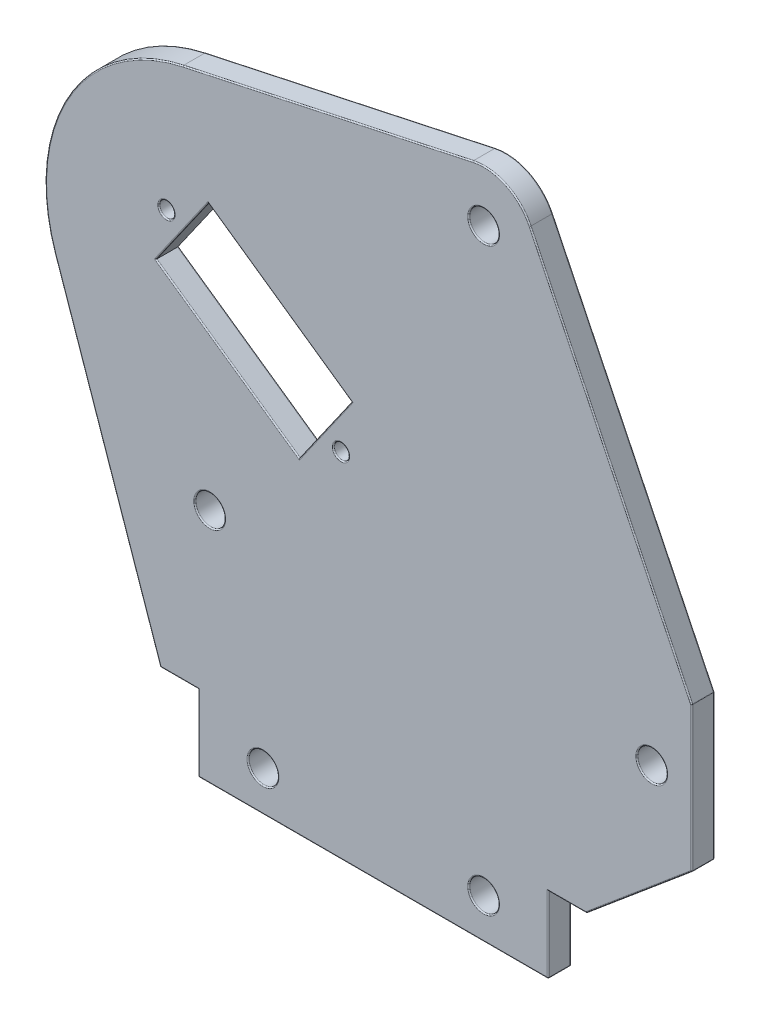
SolidWorks part; units mm, degrees
ref_plane "Płaszczyzna przednia" through (0, 0, 0) normal (0, 0, 1) x (1, 0, 0)
ref_plane "Płaszczyzna górna" through (0, 0, 0) normal (0, 1, 0) x (1, 0, 0)
ref_plane "Płaszczyzna prawa" through (0, 0, 0) normal (1, 0, 0) x (0, 0, -1)
sketch "Szkic1" plane through (0, 0, 0) normal (0, 0, 1) x (1, 0, 0)
  line L0 (28, 10) -> (41.85, 21.6215) construction
  line L1 (23, 10) -> (28, 10) construction
  line L2 (23, 0) -> (23, 10) construction
  line L3 (-23, 0) -> (23, 0) construction
  line L4 (-23, 0) -> (-23, 10) construction
  line L5 (-23, 10) -> (-28, 10) construction
  line L6 (-28, 10) -> (-41.8438, 50.1182) construction
  line L7 (28, 10) -> (41.85, 21.6215)
  line L8 (23, 10) -> (28, 10)
  line L9 (23, 0) -> (23, 10)
  line L10 (-23, 0) -> (23, 0)
  line L11 (-23, 0) -> (-23, 10)
  line L12 (-23, 10) -> (-28, 10)
  line L13 (-28, 10) -> (-41.8438, 50.1182)
  line L14 (41.85, 21.6215) -> (41.85, 40.6215) construction
  line L15 (41.85, 40.6215) -> (20.6106, 84.4605) construction
  line L16 (-25.0297, 79.9436) -> (13.0723, 88.1382) construction
  line L17 (-25.0297, 79.9436) -> (13.0723, 88.1382)
  line L18 (41.85, 40.6215) -> (20.6106, 84.4605)
  line L19 (41.85, 21.6215) -> (41.85, 40.6215)
  line L20 (0, 0) -> (0, 10) construction
  line L21 (-21.6935, 65.9364) -> (-28.5764, 56.1065)
  line L22 (-21.6935, 65.9364) -> (-2.853, 52.7441)
  line L23 (-28.5764, 56.1065) -> (-9.7359, 42.9143)
  line L24 (-2.853, 52.7441) -> (-9.7359, 42.9143)
  line L25 (-6.2944, 47.8292) -> (-25.1349, 61.0215) construction
  line L26 (-15.7147, 54.4253) -> (-19.1561, 49.5104) construction
  arc A0 (20.6106, 84.4605) -> (13.0723, 88.1382) centre (14.5, 81.5) ccw construction
  arc A1 (-25.0297, 79.9436) -> (-41.8438, 50.1182) centre (-20.22, 57.58) ccw construction
  arc A2 (-25.0297, 79.9436) -> (-41.8438, 50.1182) centre (-20.22, 57.58) ccw
  arc A3 (20.6106, 84.4605) -> (13.0723, 88.1382) centre (14.5, 81.5) ccw
  circle A4 centre (-27.1828, 62.4554) radius 1
  circle A5 centre (-4.2465, 46.3953) radius 1
  point P9 (-14.5, 5.25)
  point P10 (14.5, 5.25)
  point P11 (36.6, 31.1215)
  point P12 (-21.5, 31.1215)
  point P16 (14.5, 81.5)
  point P20 (41.85, 31.1215)
  point P26 (-20.22, 57.58)
  dimension "D9" = 2
  dimension "D1" = 5.25
  dimension "D2" = 5.25
  dimension "D3" = 21.5
  dimension "D4" = 23
  dimension "D5" = 12
  dimension "D6" = 35
  dimension "D7" = 6
  dimension "D8" = 2.5
extrude "Dodanie-wyciągnięcie1" add sketch "Szkic1" along normal blind 3
hole_wizard "Otwór pod śrubę M3.51" positions "Szkic3" profile "Szkic4" hole size "M3.5" standard "ISO" end condition through all
sketch "Szkic3" plane through (0, 0, 3) normal (0, 0, 1) x (1, 0, 0)
  point P0 (14.5, 81.5)
  point P3 (36.6, 31.1215)
  point P6 (-21.5, 31.1215)
  point P9 (14.5, 5.25)
  point P12 (-14.5, 5.25)
sketch "Szkic4" plane through (14.5, 81.5, 3) normal (1, 0, 0) x (0, -1, 0)
  line L0 (0, 0) -> (0, 3)
  line L1 (0, 3) -> (1.95, 3)
  line L2 (1.95, 3) -> (1.95, 0)
  line L5 (1.95, 0) -> (0, 0)
  line L11 (0, -6.35) -> (0, 107.95) construction
  dimension "Średnica otworu na wylot" = 3.9
  dimension "Głębokość otworu na wylot" = 3
fillet "Zaokrąglenie1" radius 0.15 52 edges at (16.45, 81.5, 3) (16.45, 81.5, 0) (38.55, 31.1215, 3) (38.55, 31.1215, 0) (-19.55, 31.1215, 3) (-19.55, 31.1215, 0) (16.45, 5.25, 3) (16.45, 5.25, 0) (-12.55, 5.25, 3) (-12.55, 5.25, 0) (-5.2465, 46.3953, 0) (-5.2465, 46.3953, 3) (-26.1828, 62.4554, 0) (-26.1828, 62.4554, 3) (-12.2732, 59.3402, 0) (-25.1349, 61.0215, 0) (-19.1561, 49.5104, 0) (-6.2944, 47.8292, 0) (-12.2732, 59.3402, 3) (-25.1349, 61.0215, 3) (-19.1561, 49.5104, 3) (-6.2944, 47.8292, 3) (25.5, 10, 0) (34.925, 15.8108, 0) (41.85, 31.1215, 0) (31.2303, 62.541, 0) (17.4772, 87.6025, 0) (-5.9787, 84.0409, 0) (-40.1467, 68.8136, 0) (-34.9219, 30.0591, 0) (-25.5, 10, 0) (-23, 5, 0) (0, 0, 0) (23, 5, 0) (25.5, 10, 3) (34.925, 15.8108, 3) (41.85, 31.1215, 3) (31.2303, 62.541, 3) (17.4772, 87.6025, 3) (-5.9787, 84.0409, 3) (-40.1467, 68.8136, 3) (-34.9219, 30.0591, 3) (-25.5, 10, 3) (-23, 5, 3) (0, 0, 3) (23, 5, 3) (-23, 0, 1.5) (-28, 10, 1.5) (41.85, 40.6215, 1.5) (41.85, 21.6215, 1.5) (28, 10, 1.5) (23, 0, 1.5)
